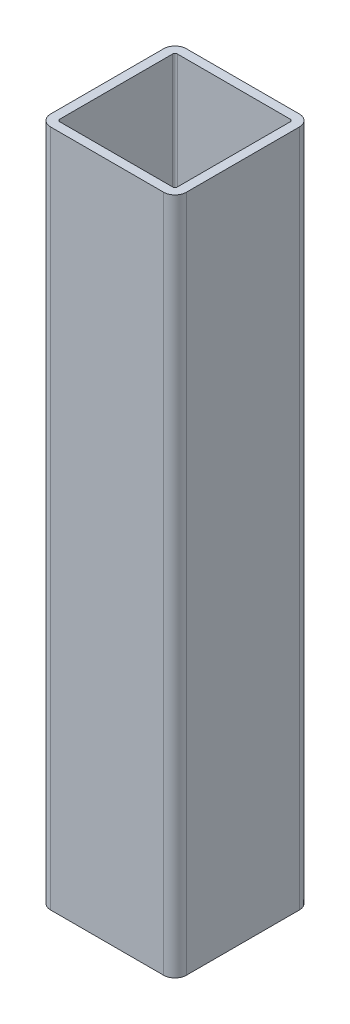
SolidWorks part; units mm, degrees
ref_plane "Front Plane" through (0, 0, 0) normal (0, 0, 1) x (1, 0, 0)
ref_plane "Top Plane" through (0, 0, 0) normal (0, 1, 0) x (1, 0, 0)
ref_plane "Right Plane" through (0, 0, 0) normal (1, 0, 0) x (0, 0, -1)
sketch "Sketch1" plane through (0, 0, 0) normal (0, 1, 0) x (1, 0, 0)
  line L1 (-15.875, 19.05) -> (15.875, 19.05)
  line L2 (-19.05, 15.875) -> (-19.05, -15.875)
  line L3 (-15.875, -19.05) -> (15.875, -19.05)
  line L4 (19.05, 15.875) -> (19.05, -15.875)
  line L5 (-19.05, 19.05) -> (19.05, -19.05) construction
  line L6 (-19.05, -19.05) -> (19.05, 19.05) construction
  arc A0 (-19.05, -15.875) -> (-15.875, -19.05) centre (-15.875, -15.875) ccw
  arc A1 (15.875, -19.05) -> (19.05, -15.875) centre (15.875, -15.875) ccw
  arc A2 (19.05, 15.875) -> (15.875, 19.05) centre (15.875, 15.875) ccw
  arc A3 (-15.875, 19.05) -> (-19.05, 15.875) centre (-15.875, 15.875) ccw
  point P0 (0, 0)
  dimension "D3" = 3.175
  dimension "D1" = 38.1
  dimension "D2" = 38.1
extrude "Extrude-Thin1" add sketch "Sketch1" along normal mid plane 190.5 thin
